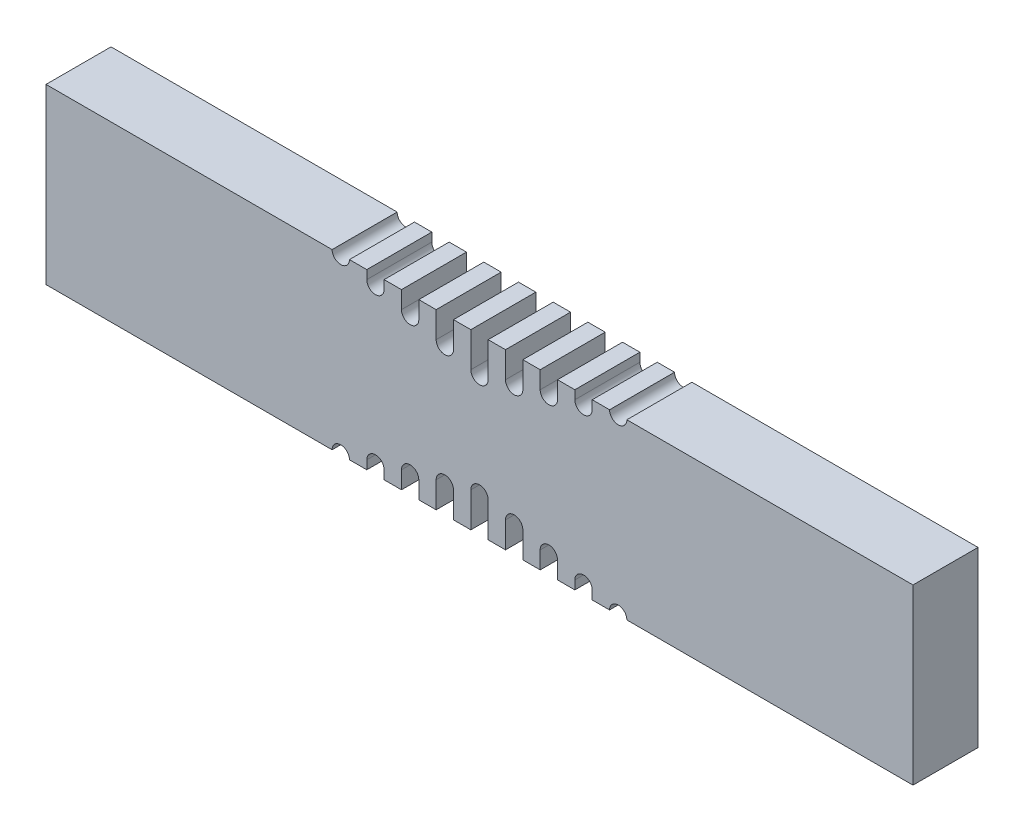
SolidWorks part; units mm, degrees
ref_plane "Front" through (0, 0, 0) normal (0, 0, 1) x (1, 0, 0)
ref_plane "Top" through (0, 0, 0) normal (0, 1, 0) x (1, 0, 0)
ref_plane "Right" through (0, 0, 0) normal (1, 0, 0) x (0, 0, -1)
sketch "Sketch1" plane through (0, 0, 0) normal (0, 0, 1) x (1, 0, 0)
  line L1 (-100, 20) -> (100, 20)
  line L2 (-100, 20) -> (-100, -20)
  line L3 (-100, -20) -> (100, -20)
  line L4 (100, 20) -> (100, -20)
  dimension "D1" = 200
  dimension "D2" = 40
  dimension "D3" = 20
  dimension "D4" = 100
extrude "Rectangular Bar (40 W x 200 L x 15D)" add sketch "Sketch1" along normal blind 15
sketch "Notch" plane through (0, 0, 15) normal (0, 0, 1) x (1, 0, 0)
  line L0 (2, 20) -> (2, 12)
  line L1 (100, 20) -> (-100, 20) construction
  line L2 (-2, -20) -> (-2, -12)
  line L3 (-2, 20) -> (-2, 12)
  line L4 (-100, -20) -> (100, -20) construction
  line L5 (2, -20) -> (2, -12)
  line L6 (-2, -20) -> (2, -20)
  line L7 (-2, 20) -> (2, 20)
  arc A0 (2, 12) -> (-2, 12) centre (0, 12) cw
  arc A1 (-2, -12) -> (2, -12) centre (0, -12) cw
  dimension "D2" = 2
  dimension "D4" = 8
  dimension "D1" = 8
  dimension "D3" = 2
  dimension "D5" = 8
extrude "Notch cut out" cut sketch "Notch" against normal blind 15
sketch "Sketch2" plane through (0, 0, 15) normal (0, 0, 1) x (1, 0, 0)
  line L0 (6, 20) -> (6, 14)
  line L1 (100, 20) -> (2, 20) construction
  line L2 (10, 20) -> (10, 14)
  line L3 (14, 20) -> (14, 16)
  line L4 (18, 20) -> (18, 16)
  line L5 (22, 20) -> (22, 18)
  line L6 (26, 20) -> (26, 18)
  line L7 (6, 20) -> (10, 20)
  line L8 (14, 20) -> (18, 20)
  line L9 (22, 20) -> (26, 20)
  line L10 (30, 20) -> (34, 20)
  line L11 (0, 0) -> (0, 66.7026) construction
  line L12 (-30, 20) -> (-34, 20)
  line L13 (-22, 20) -> (-26, 20)
  line L14 (-26, 20) -> (-26, 18)
  line L15 (-22, 20) -> (-22, 18)
  line L16 (-18, 20) -> (-18, 16)
  line L17 (-14, 20) -> (-14, 16)
  line L18 (-14, 20) -> (-18, 20)
  line L19 (-10, 20) -> (-10, 14)
  line L20 (-6, 20) -> (-6, 14)
  line L21 (-6, 20) -> (-10, 20)
  line L22 (-140.4853, 0) -> (170.8447, 0) construction
  line L23 (30, -20) -> (34, -20)
  line L24 (26, -20) -> (26, -18)
  line L25 (22, -20) -> (22, -18)
  line L26 (22, -20) -> (26, -20)
  line L27 (18, -20) -> (18, -16)
  line L28 (14, -20) -> (14, -16)
  line L29 (14, -20) -> (18, -20)
  line L30 (10, -20) -> (10, -14)
  line L31 (6, -20) -> (6, -14)
  line L32 (6, -20) -> (10, -20)
  line L33 (-6, -20) -> (-6, -14)
  line L34 (-10, -20) -> (-10, -14)
  line L35 (-6, -20) -> (-10, -20)
  line L36 (-14, -20) -> (-14, -16)
  line L37 (-18, -20) -> (-18, -16)
  line L38 (-14, -20) -> (-18, -20)
  line L39 (-30, -20) -> (-34, -20)
  line L40 (-22, -20) -> (-22, -18)
  line L41 (-22, -20) -> (-26, -20)
  line L42 (-26, -20) -> (-26, -18)
  arc A1 (6, 14) -> (10, 14) centre (8, 14) ccw
  arc A2 (14, 16) -> (18, 16) centre (16, 16) ccw
  arc A3 (22, 18) -> (26, 18) centre (24, 18) ccw
  arc A4 (34, 20) -> (30, 20) centre (32, 20) cw
  arc A5 (-34, 20) -> (-30, 20) centre (-32, 20) ccw
  arc A6 (-22, 18) -> (-26, 18) centre (-24, 18) cw
  arc A7 (-14, 16) -> (-18, 16) centre (-16, 16) cw
  arc A8 (-6, 14) -> (-10, 14) centre (-8, 14) cw
  arc A9 (34, -20) -> (30, -20) centre (32, -20) ccw
  arc A10 (22, -18) -> (26, -18) centre (24, -18) cw
  arc A11 (14, -16) -> (18, -16) centre (16, -16) cw
  arc A12 (6, -14) -> (10, -14) centre (8, -14) cw
  arc A13 (-6, -14) -> (-10, -14) centre (-8, -14) ccw
  arc A14 (-14, -16) -> (-18, -16) centre (-16, -16) ccw
  arc A15 (-22, -18) -> (-26, -18) centre (-24, -18) ccw
  arc A16 (-34, -20) -> (-30, -20) centre (-32, -20) cw
  dimension "D13" = 32
  dimension "D1" = 6
  dimension "D2" = 4
  dimension "D3" = 4
  dimension "D4" = 2
  dimension "D5" = 2
  dimension "D6" = 6
  dimension "D7" = 6
  dimension "D8" = 10
  dimension "D9" = 14
  dimension "D10" = 18
  dimension "D11" = 22
  dimension "D12" = 26
extrude "Cut-Extrude1" cut sketch "Sketch2" against normal through all
